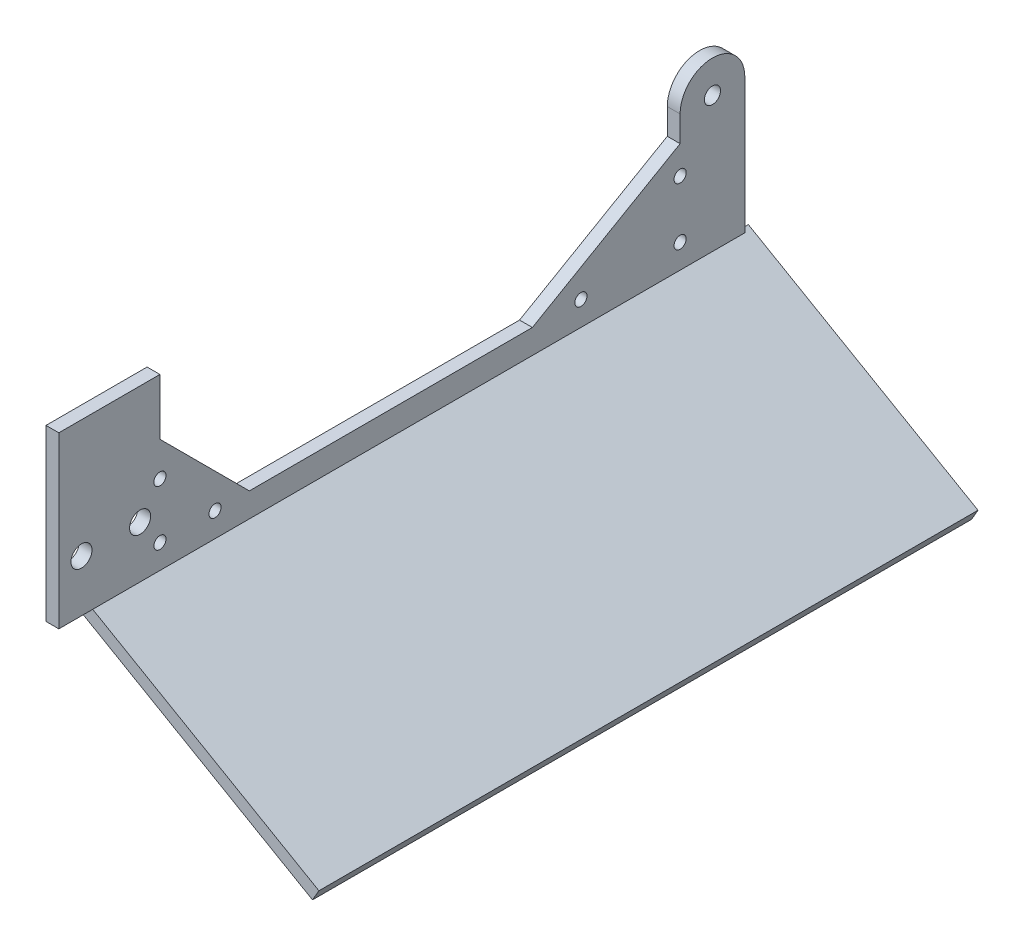
SolidWorks part; units mm, degrees
ref_plane "Front Plane" through (0, 0, 0) normal (0, 0, 1) x (1, 0, 0)
ref_plane "Top Plane" through (0, 0, 0) normal (0, 1, 0) x (1, 0, 0)
ref_plane "Right Plane" through (0, 0, 0) normal (1, 0, 0) x (0, 0, -1)
sketch "Sketch6" plane through (0, 0, 0) normal (0, 1, 0) x (1, 0, 0)
  line L0 (0, -218.7522) -> (0, 116.8814) construction
sketch "Sketch9" plane through (0, 0, 0) normal (1, 0, 0) x (0, 0, -1)
  line L0 (37.6238, 70.8385) -> (37.6238, 7.9992) construction
  line L1 (51.1496, 71.1243) -> (51.1496, 8.285) construction
  line L2 (65.9911, 71.1243) -> (65.9911, 8.285) construction
  line L3 (79.3028, 71.1243) -> (79.3028, 8.2774) construction
  line L4 (93.104, 70.9385) -> (93.104, 8.0915) construction
  line L5 (108.8651, 7.9915) -> (108.8651, 70.8446) construction
  line L6 (126.2304, 71.1243) -> (126.2304, 8.2774) construction
  line L7 (134.6212, 7.9657) -> (134.6212, 70.8175) construction
  line L8 (19.8849, 61.8648) -> (19.8849, 60.5648) construction
  line L9 (19.8849, 61.8648) -> (140.5349, 61.8648) construction
  line L10 (19.8849, 11.0648) -> (140.5349, 11.0648) construction
  line L11 (19.8849, 60.5648) -> (19.8849, 56.9648) construction
  line L12 (19.8849, 36.4648) -> (140.5349, 36.4648) construction
  line L13 (19.8849, 47.4648) -> (140.5349, 47.4648) construction
  line L14 (19.8849, 25.4648) -> (140.5349, 25.4648) construction
  line L15 (19.8849, 15.9648) -> (140.5349, 15.9648) construction
  line L16 (19.8849, 56.9648) -> (140.5349, 56.9648) construction
  line L17 (24.4126, 70.8385) -> (24.4126, 7.9992)
  line L18 (19.8849, 12.3648) -> (140.5349, 12.3648) construction
  line L19 (19.8849, 60.5648) -> (140.5349, 60.5648) construction
  line L20 (140.5349, 61.8648) -> (140.5349, 60.5648) construction
  line L21 (-218.7522, 0) -> (116.8814, 0) construction
  line L22 (140.5349, 60.5648) -> (140.5349, 56.9648) construction
  line L23 (140.5349, 56.9648) -> (140.5349, 47.4648) construction
  line L24 (140.5349, 47.4648) -> (140.5349, 36.4648) construction
  line L25 (140.5349, 36.4648) -> (140.5349, 25.4648) construction
  line L26 (140.5349, 25.4648) -> (140.5349, 15.9648) construction
  line L27 (140.5349, 15.9648) -> (140.5349, 12.3648) construction
  line L28 (140.5349, 12.3648) -> (140.5349, 11.0648) construction
  line L29 (19.8849, 56.9648) -> (19.8849, 47.4648) construction
  line L30 (19.8849, 47.4648) -> (19.8849, 36.4648) construction
  line L31 (19.8849, 36.4648) -> (19.8849, 25.4648) construction
  line L32 (19.8849, 25.4648) -> (19.8849, 15.9648) construction
  line L33 (19.8849, 15.9648) -> (19.8849, 12.3648) construction
  line L34 (19.8849, 12.3648) -> (19.8849, 11.0648) construction
  spline S0 degree 3 poles (51.2996, 60.9306) (65.3231, 61.9876) (79.6239, 62.1542) (93.583, 60.8224) (110.3999, 56.9428) (123.3769, 51.8767) (135.0763, 45.9483) (143.4183, 36.2774) (135.0505, 27.8617) (123.4214, 21.8328) (110.225, 15.7356) (93.6714, 12.1328) (79.5289, 10.8674) (65.4121, 10.9017) (51.0743, 12.0654) (37.6053, 14.9428) (23.9138, 23.9186) (18.0793, 36.4535) (24.0546, 49.1584) (37.259, 57.8231) (51.2996, 60.9306) (65.3231, 61.9876) (79.6239, 62.1542) knots -0.161453 -0.105693 -0.054332 0 0.047894 0.097672 0.154194 0.222755 0.257069 0.295416 0.33342 0.367649 0.435779 0.492752 0.542693 0.590587 0.644732 0.696926 0.751601 0.795074 0.838547 0.894307 0.945668 1 1.047894 1.097672 1.154194 only from (65.9911, 61.8648) to (65.9911, 61.8648)
  dimension "D10" = 11.0648
  dimension "D1" = 50.8
  dimension "D2" = 120.65
  dimension "D3" = 11
  dimension "D4" = 11
  dimension "D5" = 20.5
  dimension "D6" = 20.5
  dimension "D7" = 24.1
  dimension "D8" = 24.1
ref_plane "Plane3" through (0, 0, 0) normal (-0.5, -0.866, 0) x (0, 0, -1)
sketch "Sketch10" plane through (0, 0, 0) normal (1, 0, 0) x (0, 0, -1)
  line L0 (15.8849, 36.4648) -> (0, 36.4648)
  line L1 (0, 36.4648) -> (0, 0)
  line L2 (-218.7522, 0) -> (116.8814, 0) construction
  line L3 (0, 0) -> (163, 0)
  line L4 (111.8843, 0) -> (-111.8843, 0) construction
  line L5 (163, 0) -> (163, 15)
  line L7 (144.5349, 36.4648) -> (144.5349, 30.0934)
  line L8 (144.5349, 30.0934) -> (108, 9)
  line L9 (108, 9) -> (38, 9)
  line L10 (38, 9) -> (15.8849, 31.1151)
  line L11 (15.8849, 31.1151) -> (15.8849, 36.4648)
  line L12 (144.5349, 36.4648) -> (144.5349, 40)
  line L15 (153, 20) -> (163, 15)
  line L16 (153, 40) -> (153, 0) construction
  line L17 (140.5349, 36.4648) -> (163, 36.4648) construction
  line L21 (163, 40) -> (163, 28)
  line L22 (163, 28) -> (159, 28)
  line L23 (159, 28) -> (158, 30.0934)
  line L24 (158, 30.0934) -> (153, 30.0934)
  line L25 (153, 30.0934) -> (153, 20)
  line L26 (144.5349, 40) -> (153, 40)
  line L27 (153, 40) -> (163, 40)
  dimension "D1" = 4
  dimension "D2" = 9
  dimension "D3" = 4
  dimension "D4" = 40
  dimension "D5" = 225
  dimension "D6" = 240
  dimension "D7" = 70
  dimension "D8" = 38
  dimension "D9" = 4
  dimension "D10" = 5
  dimension "D11" = 55
  dimension "D12" = 10
  dimension "D13" = 12
  dimension "D14" = 20
  dimension "D15" = 15
sketch "Sketch11" plane through (0, 0, 0) normal (-0.5, -0.866, 0) x (0, 0, -1)
  line L1 (163, 0) -> (0, 0)
  line L2 (163, 0) -> (163, 65.5808)
  line L3 (163, 65.5808) -> (0, 65.5808)
  line L4 (0, 0) -> (0, 65.5808)
extrude "Boss-Extrude2" add sketch "Sketch11" against normal blind 3.175 separate body
sketch "Sketch12" plane through (0, 0, 0) normal (1, 0, 0) x (0, 0, -1)
  line L0 (-9.1151, 45) -> (15.8849, 45)
  line L1 (15.8849, 45) -> (15.8849, 31.1151)
  line L4 (15.8849, 31.1151) -> (15.8849, 22.6298) construction
  line L7 (-9.1151, 34) -> (-9.1151, 0) construction
  line L8 (160.5349, 3) -> (160.5349, 36.4648)
  line L16 (144.5349, 36.4648) -> (144.5349, 30.0934)
  line L17 (144.5349, 30.0934) -> (108, 9)
  line L18 (38, 9) -> (108, 9)
  line L19 (15.8849, 22.6298) -> (15.8849, 9) construction
  line L20 (-9.1151, 3) -> (160.5349, 3)
  line L21 (-9.1151, 36.4648) -> (160.5349, 36.4648) construction
  line L22 (-6.4853, 45) -> (35.5147, 3) construction
  line L23 (160.5349, 32.4028) -> (109.6077, 3) construction
  line L24 (38, 9) -> (-9.1151, 9) construction
  line L25 (108, 9) -> (160.5349, 9) construction
  line L26 (15.8849, 9) -> (15.8849, 1.1287) construction
  line L27 (144.5349, 30.0934) -> (144.5349, 3) construction
  line L28 (15.8849, 31.1151) -> (38, 9)
  line L31 (144.5349, 36.4648) -> (160.5349, 36.4648) construction
  line L33 (19.8849, 36.4648) -> (140.5349, 36.4648) construction
  line L35 (-9.1151, 15.8149) -> (15.8849, 15.8149) construction
  line L38 (3.3849, 45) -> (3.3849, 3) construction
  line L41 (-9.1151, 45) -> (-9.1151, 3)
  line L42 (-6.1151, 15.8149) -> (-6.1151, 0) construction
  line L43 (-218.7522, 0) -> (116.8814, 0) construction
  line L44 (-9.1151, 15.8149) -> (15.8849, 15.8149) construction
  circle A0 centre (15.8849, 22.6298) radius 1.5
  circle A1 centre (120, 9) radius 1.5
  circle A2 centre (144.5349, 23.1652) radius 1.5
  circle A3 centre (29.5147, 9) radius 1.5
  circle A4 centre (15.8849, 9) radius 1.5
  circle A5 centre (144.5349, 9) radius 1.5
  circle A7 centre (152.5349, 36.4648) radius 2
  arc A8 (144.5349, 36.4648) -> (160.5349, 36.4648) centre (152.5349, 36.4648) cw
  circle A9 centre (-3.5151, 15.8149) radius 2.6
  circle A10 centre (10.9849, 15.8149) radius 2.6
  point P29 (10.9849, 15.8149)
  point P31 (-3.5151, 15.8149)
  point P32 (-2.3358, 15.8149)
  point P57 (9.3537, 17.8395)
  point P64 (0, 0)
  dimension "D1" = 3
  dimension "D2" = 6
  dimension "D4" = 4
  dimension "D7" = 5.2
  dimension "D3" = 6
  dimension "D5" = 16
  dimension "D6" = 6
  dimension "D8" = 3
  dimension "D9" = 14.5
  dimension "D10" = 42
  dimension "D11" = 4
  dimension "D12" = 225
extrude "Boss-Extrude3" add sketch "Sketch12" along normal blind 3.175 separate body
ref_plane "Plane2" through (45, 0, 0) normal (1, 0, 0) x (0, 0, -1)
sketch "Sketch5" plane through (0, 19.2012, 184.6399) normal (1, 0, 0) x (0, 0, -1)
  line L2 (204.3693, -19.2012) -> (184.3693, 4.2988)
  line L4 (184.3693, 29.2988) -> (204.3693, 52.7988)
  line L10 (131.5763, 16.7988) -> (15.8268, 16.7988) construction
  line L11 (247.3693, 5.4691) -> (247.3693, -92.3775) construction
  line L12 (204.3693, -100.7007) -> (204.3693, 68.0605) construction
  line L13 (184.3693, 4.2988) -> (184.3693, 29.2988)
  line L16 (247.3693, 42.7988) -> (265.3693, 42.7988)
  line L17 (265.3693, 42.7988) -> (265.3693, 52.7988)
  line L18 (265.3693, 52.7988) -> (204.3693, 52.7988)
  line L19 (204.3693, -19.2012) -> (265.3693, -19.2012)
  line L20 (265.3693, -19.2012) -> (265.3693, -9.2012)
  line L21 (265.3693, -9.2012) -> (247.3693, -9.2012)
  line L22 (-34.1123, -19.2012) -> (301.5213, -19.2012) construction
  ellipse E0 centre (247.3693, 16.7988) end of major axis (204.3693, 16.7988) minor radius 26 (247.3693, -9.2012) -> (247.3693, 42.7988) cw
  point P0 (184.3693, 16.7988)
  point P29 (105.2094, 0.142)
  point P34 (105.2094, -19.858)
  dimension "D2" = 20
  dimension "D7" = 25
  dimension "D1" = 26
  dimension "D3" = 43
  dimension "D4" = 10
  dimension "D5" = 10
  dimension "D6" = 18
sketch "Sketch8" plane through (0, 0, 0) normal (1, 0, 0) x (0, 0, -1)
  line L0 (318.4214, 400.3917) -> (1509.088, 400.3917) construction
